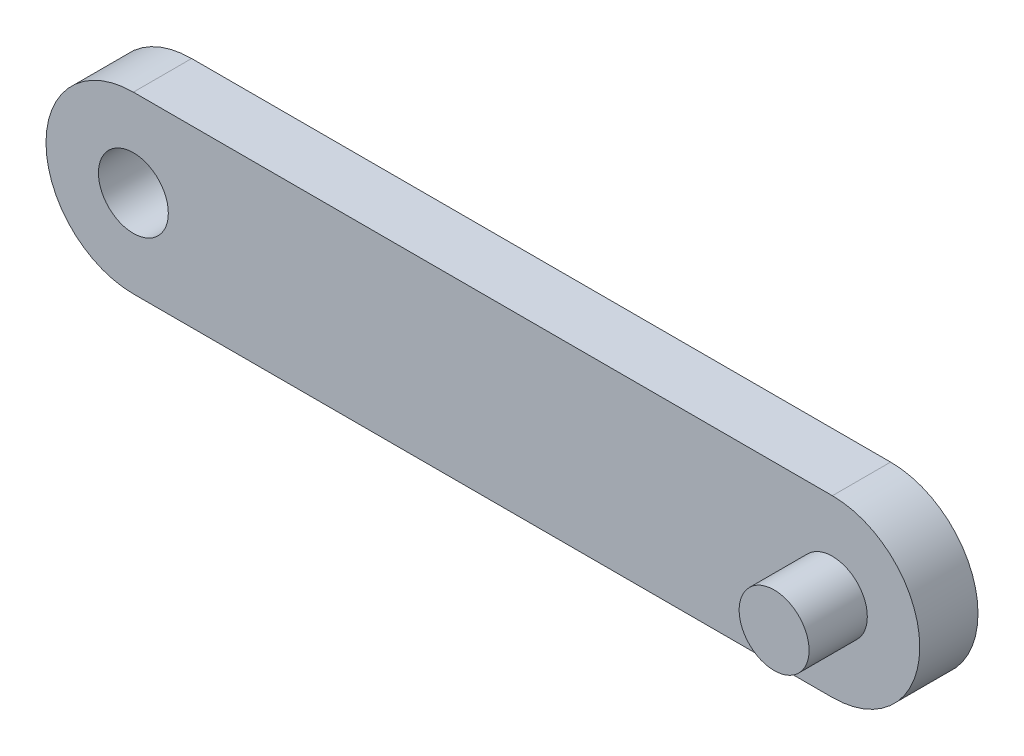
SolidWorks part; units mm, degrees
material "ABS"
ref_plane "Alzado" through (0, 0, 0) normal (0, 0, 1) x (1, 0, 0)
ref_plane "Planta" through (0, 0, 0) normal (0, 1, 0) x (1, 0, 0)
ref_plane "Vista lateral" through (0, 0, 0) normal (1, 0, 0) x (0, 0, -1)
sketch "Croquis1" plane through (0, 0, 0) normal (0, 0, 1) x (1, 0, 0)
  line L0 (0, 0) -> (120, 0) construction
  line L1 (0, 15) -> (120, 15)
  line L2 (0, -15) -> (120, -15)
  arc A0 (0, 15) -> (0, -15) centre (0, 0) ccw
  arc A1 (120, -15) -> (120, 15) centre (120, 0) ccw
  circle A2 centre (0, 0) radius 6
  point P3 (60, 0)
  dimension "D1" = 12
  dimension "D2" = 120
  dimension "D3" = 30
extrude "Saliente-Extruir1" add sketch "Croquis1" along normal blind 10
sketch "Croquis2" plane through (0, 0, 10) normal (0, 0, 1) x (1, 0, 0)
  line L0 (135, 0) -> (120, 0) construction
  arc A0 (120, -15) -> (120, 15) centre (120, 0) ccw construction
  circle A1 centre (120, 0) radius 6
  dimension "D1" = 12
extrude "Saliente-Extruir2" add sketch "Croquis2" along normal blind 10
